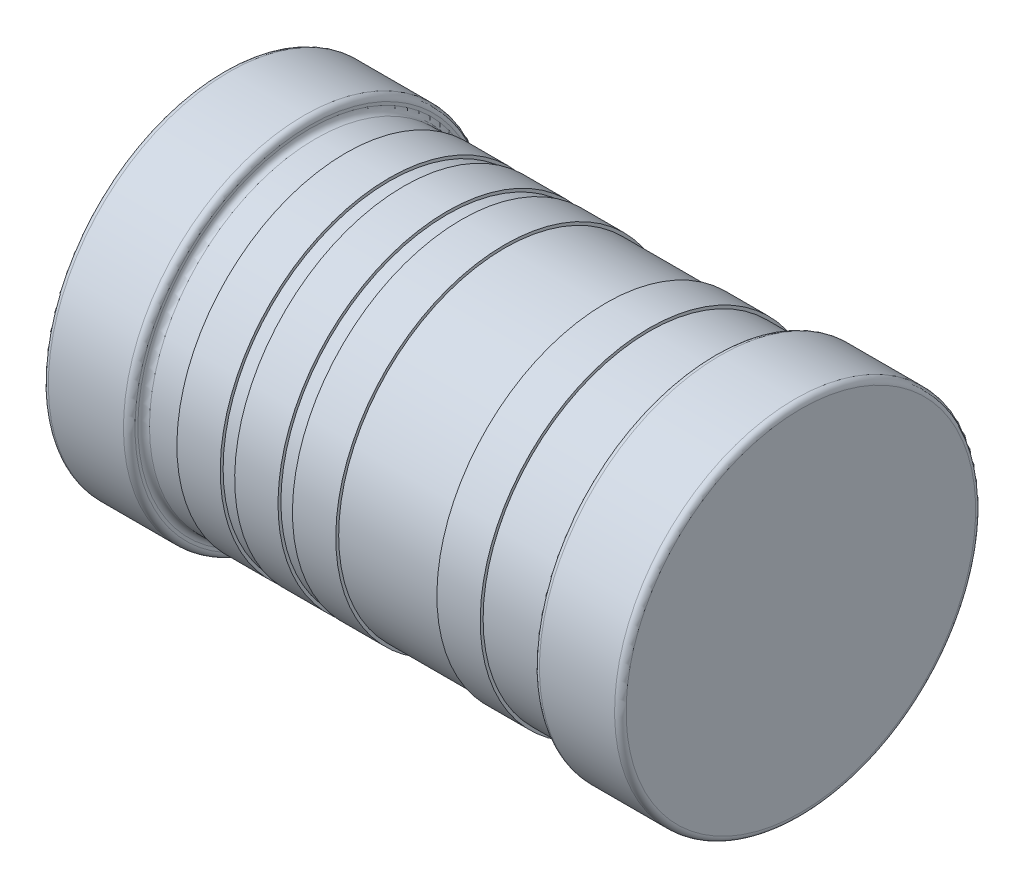
SolidWorks part; units mm, degrees
ref_plane "Front Plane" through (0, 0, 0) normal (0, 0, 1) x (1, 0, 0)
ref_plane "Top Plane" through (0, 0, 0) normal (0, 1, 0) x (1, 0, 0)
ref_plane "Right Plane" through (0, 0, 0) normal (1, 0, 0) x (0, 0, -1)
sketch "Sketch1" plane through (0, 0, 0) normal (0, 0, 1) x (1, 0, 0)
  line L0 (-1, 0.625) -> (1, 0.625)
  line L1 (0, 0) -> (0, 0.625) construction
  line L2 (-1, 0.625) -> (-3.0256, 0.625) construction
  line L3 (1, 0.625) -> (1, 0.02)
  line L4 (-0.98, 0) -> (-0.72, 0)
  line L5 (-1, 0.02) -> (-1, 0.625)
  line L6 (-0.7, 0.02) -> (-0.7, 0.03)
  line L7 (-0.68, 0.05) -> (-0.575, 0.05)
  line L8 (0.7, 0.03) -> (0.7, 0.02)
  line L9 (0.72, 0) -> (0.98, 0)
  line L10 (-0.575, 0.05) -> (-0.575, 0.04)
  line L11 (-0.575, 0.04) -> (-0.425, 0.04)
  line L12 (-0.425, 0.04) -> (-0.425, 0.05)
  line L13 (-0.375, 0.05) -> (-0.375, 0.04)
  line L14 (-0.375, 0.04) -> (-0.225, 0.04)
  line L15 (-0.225, 0.04) -> (-0.225, 0.05)
  line L16 (-0.025, 0.04) -> (-0.175, 0.04)
  line L17 (-0.175, 0.04) -> (-0.175, 0.05)
  line L18 (0.475, 0.05) -> (0.68, 0.05)
  line L19 (-0.025, 0.04) -> (-0.025, 0.05)
  line L20 (0.475, 0.05) -> (0.475, 0.04)
  line L21 (0.475, 0.04) -> (0.325, 0.04)
  line L22 (0.325, 0.04) -> (0.325, 0.05)
  line L23 (-0.5, 0.04) -> (-0.5, -0.0114) construction
  line L24 (-0.3, 0.04) -> (-0.3, -0.0114) construction
  line L25 (-0.1, 0.04) -> (-0.1, -0.0151) construction
  line L26 (0.4, 0.04) -> (0.4, -0.0151) construction
  line L27 (-0.025, 0.05) -> (0.325, 0.05)
  line L28 (-0.225, 0.05) -> (-0.175, 0.05)
  line L29 (-0.425, 0.05) -> (-0.375, 0.05)
  arc A0 (1, 0.02) -> (0.98, 0) centre (0.98, 0.02) cw
  arc A1 (0.72, 0) -> (0.7, 0.02) centre (0.72, 0.02) cw
  arc A2 (0.7, 0.03) -> (0.68, 0.05) centre (0.68, 0.03) ccw
  arc A3 (-0.68, 0.05) -> (-0.7, 0.03) centre (-0.68, 0.03) ccw
  arc A4 (-0.7, 0.02) -> (-0.72, 0) centre (-0.72, 0.02) cw
  arc A5 (-1, 0.02) -> (-0.98, 0) centre (-0.98, 0.02) ccw
  point P15 (1, 0)
  point P18 (0.7, 0)
  dimension "D5" = 0.02
  dimension "D1" = 2
  dimension "D2" = 0.3
  dimension "D3" = 0.05
  dimension "D4" = 0.625
  dimension "D6" = 0.15
  dimension "D7" = 0.01
  dimension "D8" = 0.2
  dimension "D9" = 0.2
  dimension "D10" = 0.1
  dimension "D11" = 0.4
revolve "Revolve1" add sketch "Sketch1" angle 360 about L2
